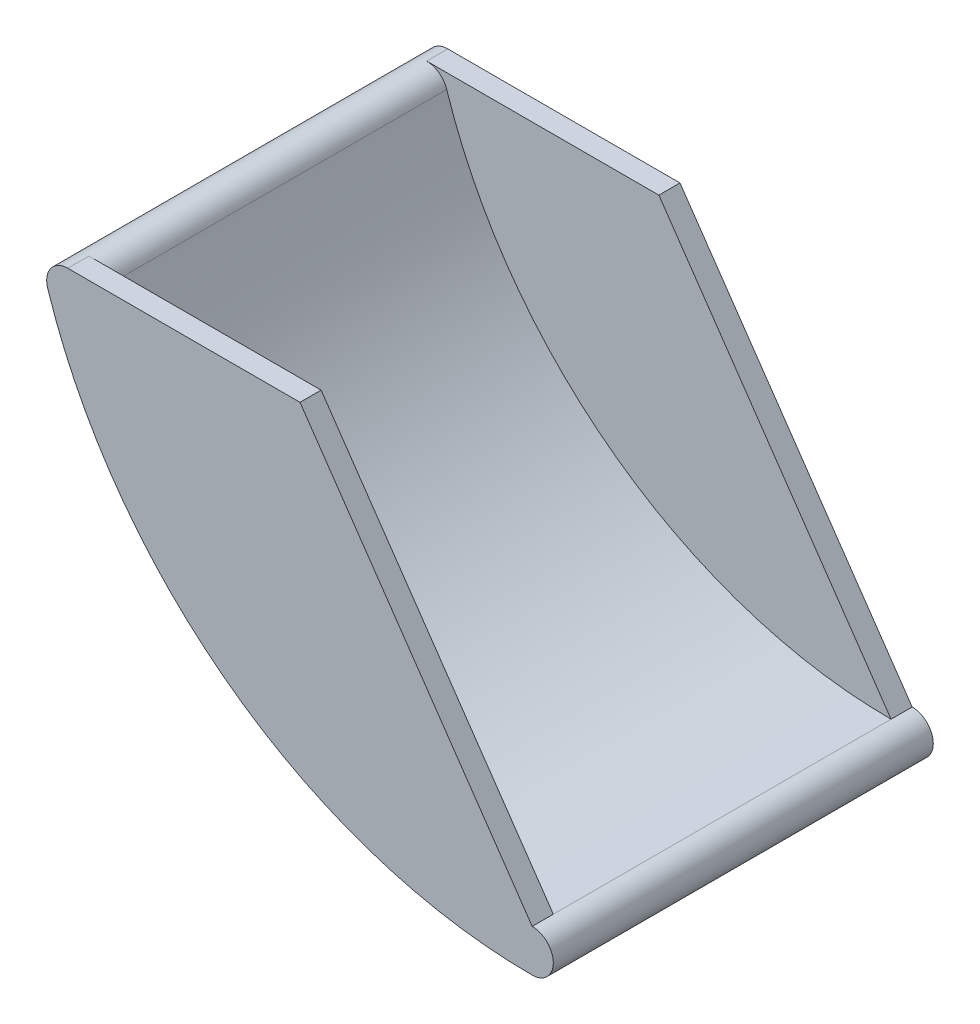
SolidWorks part; units mm, degrees
ref_plane "Front Plane" through (0, 0, 0) normal (0, 0, 1) x (1, 0, 0)
ref_plane "Top Plane" through (0, 0, 0) normal (0, 1, 0) x (1, 0, 0)
ref_plane "Right Plane" through (0, 0, 0) normal (1, 0, 0) x (0, 0, -1)
sketch "Sketch1" plane through (0, 0, 0) normal (0, 0, 1) x (1, 0, 0)
  line L0 (0, 0) -> (0, 160)
  line L1 (0, 0) -> (220, 0)
  arc A0 (0, 160) -> (220, 0) centre (220, 231.25) ccw
  arc A1 (220, 0) -> (0, 160) centre (220, 231.25) cw construction
  arc A2 (-9.5135, 156.9189) -> (220, -10) centre (220, 231.25) ccw
  arc A3 (9.5135, 163.0811) -> (220, 10) centre (220, 231.25) ccw
  arc A4 (9.5135, 163.0811) -> (-9.5135, 156.9189) centre (0, 160) ccw
  arc A5 (220, -10) -> (220, 10) centre (220, 0) ccw
  point P6 (83.9853, 44.2298)
  dimension "D3" = 10
  dimension "D1" = 160
  dimension "D2" = 220
extrude "Base" add sketch "Sketch1" along normal mid plane 180 contours A2 A5 A3 A4 L0 A0 L1 | L0 A2 L1 A0
ref_plane "Plane5" through (0, 0, 80) normal (0, 0, 1) x (1, 0, 0)
ref_plane "Plane6" through (0, 0, 0) normal (0, 0, -1) x (-1, 0, 0)
sketch "Sketch3" plane through (0, 0, 80) normal (0, 0, 1) x (1, 0, 0)
  line L0 (0, 170) -> (220, 170)
  line L1 (220, 170) -> (220, 10)
  arc A1 (9.5135, 163.0811) -> (220, 10) centre (220, 231.25) ccw construction
  arc A2 (9.5135, 163.0811) -> (-9.5135, 156.9189) centre (0, 160) ccw construction
  arc A4 (9.5135, 163.0811) -> (220, 10) centre (220, 231.25) ccw
  arc A5 (9.5135, 163.0811) -> (0, 170) centre (0, 160) ccw
  point P10 (230, 170)
  point P11 (230, 0)
  point P12 (230, 0)
  point P13 (0, 0)
  point P14 (221.4264, 10)
extrude "Wall" add sketch "Sketch3" along normal blind 10
mirror "Mirror4" about plane through (0, 0, 0) normal (0, 0, -1) of "Wall"
sketch "Sketch5" plane through (0, 0, 90) normal (0, 0, 1) x (1, 0, 0)
  line L0 (220, 10) -> (110, 170)
  line L1 (220, 170) -> (0, 170) construction
  line L2 (110, 170) -> (220, 170)
  line L3 (220, 170) -> (220, 10)
extrude "Cut-Extrude2" cut sketch "Sketch5" against normal through all
